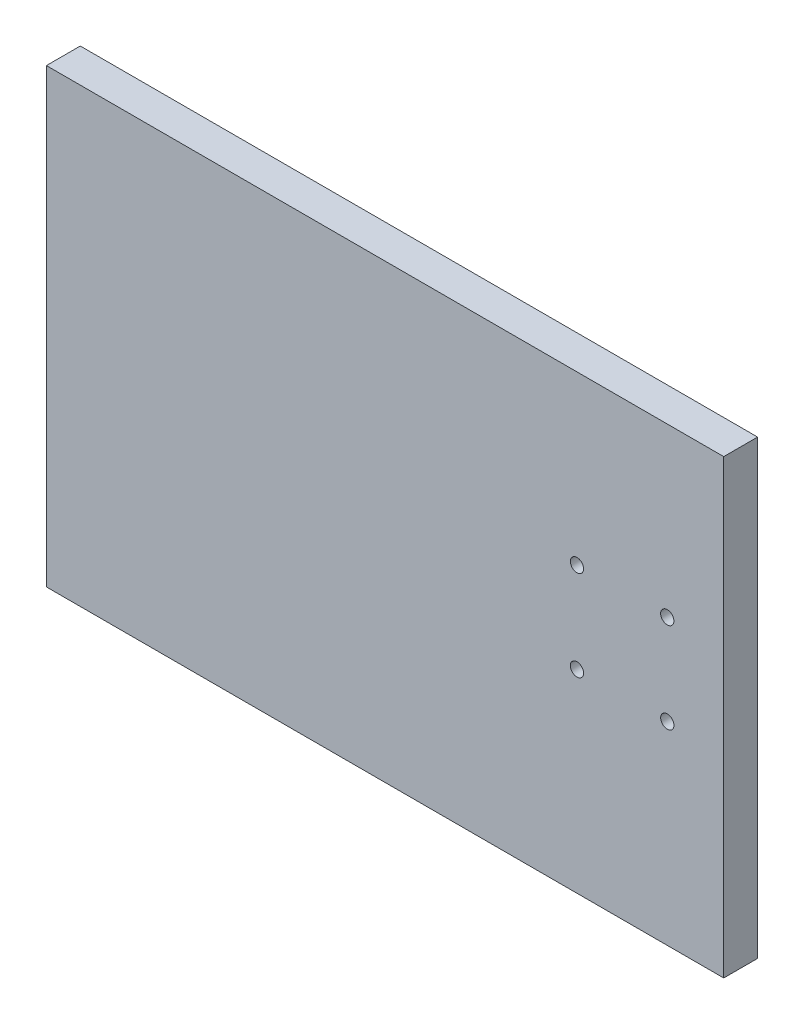
SolidWorks part; units mm, degrees
ref_plane "Plan de face" through (0, 0, 0) normal (0, 0, 1) x (1, 0, 0)
ref_plane "Plan de dessus" through (0, 0, 0) normal (0, 1, 0) x (1, 0, 0)
ref_plane "Plan de droite" through (0, 0, 0) normal (1, 0, 0) x (0, 0, -1)
sketch "Esquisse1" plane through (0, 0, 0) normal (0, 0, 1) x (1, 0, 0)
  line L1 (-64.0159, 42.1859) -> (55.9841, 42.1859)
  line L2 (-64.0159, 42.1859) -> (-64.0159, -37.8141)
  line L3 (-64.0159, -37.8141) -> (55.9841, -37.8141)
  line L4 (55.9841, 42.1859) -> (55.9841, -37.8141)
  dimension "D1" = 80
  dimension "D2" = 120
extrude "Boss.-Extru.1" add sketch "Esquisse1" along normal blind 6
sketch "Esquisse2" plane through (0, 0, 6) normal (0, 0, 1) x (1, 0, 0)
  line L0 (55.9841, -37.8141) -> (55.9841, 42.1859) construction
  line L1 (55.9841, 42.1859) -> (-64.0159, 42.1859) construction
  circle A0 centre (45.9841, 12.5359) radius 1.175
  circle A1 centre (29.9841, 12.5359) radius 1.175
  circle A2 centre (29.9841, -3.4641) radius 1.175
  circle A3 centre (45.9841, -3.4641) radius 1.175
  dimension "D7" = 2.35
  dimension "D8" = 2.35
  dimension "D9" = 2.35
  dimension "D10" = 2.35
  dimension "D1" = 10
  dimension "D2" = 10
  dimension "D3" = 16
  dimension "D4" = 16
  dimension "D5" = 16
  dimension "D6" = 16
  dimension "D11" = 29.65
  dimension "D12" = 29.65
extrude "Enlèv. mat.-Extru.1" cut sketch "Esquisse2" against normal blind 6
